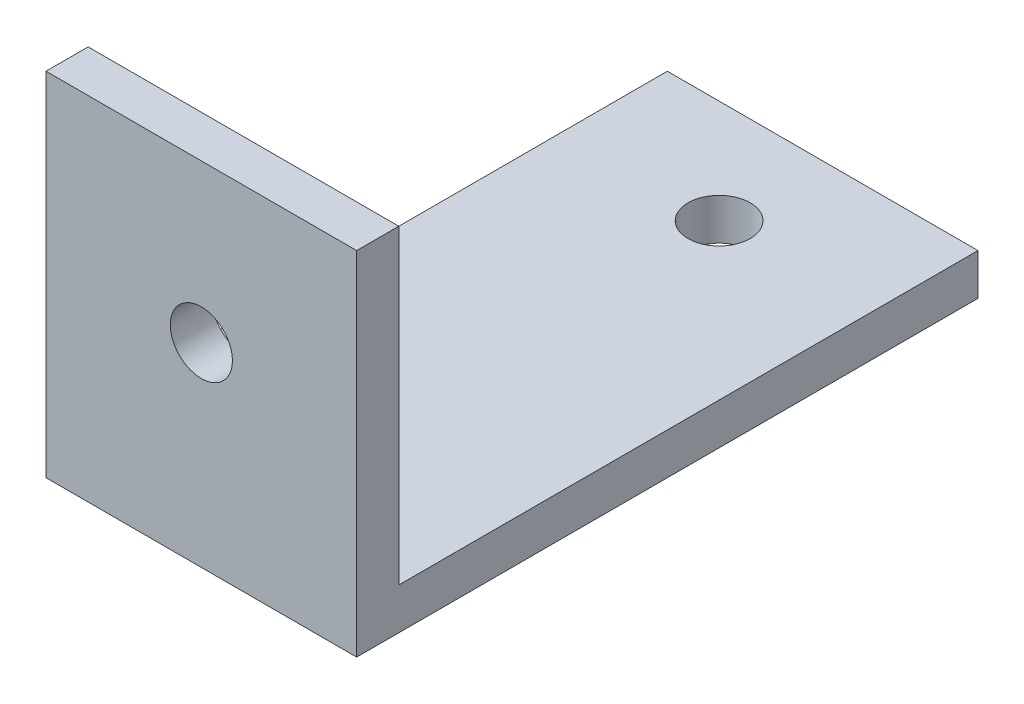
SolidWorks part; units mm, degrees
ref_plane "Front Plane" through (0, 0, 0) normal (0, 0, 1) x (1, 0, 0)
ref_plane "Top Plane" through (0, 0, 0) normal (0, 1, 0) x (1, 0, 0)
ref_plane "Right Plane" through (0, 0, 0) normal (1, 0, 0) x (0, 0, -1)
sketch "Sketch1" plane through (0, 0, 0) normal (0, 1, 0) x (1, 0, 0)
  line L0 (-14.2375, 6.8837) -> (-14.2375, 50006.8837) construction
  line L1 (-14.2375, -8.1163) -> (-29.2375, -8.1163)
  line L2 (-14.2375, -8.1163) -> (-14.2375, 21.8837)
  line L3 (-14.2375, 21.8837) -> (-29.2375, 21.8837)
  line L4 (-29.2375, -8.1163) -> (-29.2375, 21.8837)
  line L5 (-1029.2375, 6.8837) -> (48970.7625, 6.8837) construction
  line L6 (-21.7375, -978.1163) -> (-21.7375, 49021.8837) construction
  circle A0 centre (-21.7375, 16.8837) radius 1.5
  circle A1 centre (-21.7375, -3.1163) radius 1.5
  point P7 (-14.2375, 6.8837)
  point P10 (-29.2375, 6.8837)
  point P13 (-21.7375, 21.8837)
  dimension "D3" = 10
  dimension "D1" = 15
  dimension "D2" = 30
  dimension "D4" = 10
extrude "Boss-Extrude1" add sketch "Sketch1" along normal blind 2
sketch "Sketch3" plane through (0, 2, 0) normal (0, 1, 0) x (1, 0, 0)
  line L0 (-29.2375, 21.8837) -> (-29.2375, -8.1163) construction
  line L1 (-29.2375, -6.0815) -> (-14.2375, -6.0815)
  line L2 (-29.2375, -6.0815) -> (-29.2375, -8.1163)
  line L3 (-29.2375, -8.1163) -> (-14.2375, -8.1163)
  line L4 (-14.2375, -6.0815) -> (-14.2375, -8.1163)
extrude "Boss-Extrude2" add sketch "Sketch3" along normal blind 15
sketch "Sketch4" plane through (0, 0, 6.0815) normal (0, 0, -1) x (-1, 0, 0)
  line L0 (14.2375, 17) -> (14.2375, 2) construction
  circle A0 centre (21.7375, 9.3982) radius 1.5
  dimension "D1" = 7.5
extrude "Cut-Extrude1" cut sketch "Sketch4" against normal blind 15
